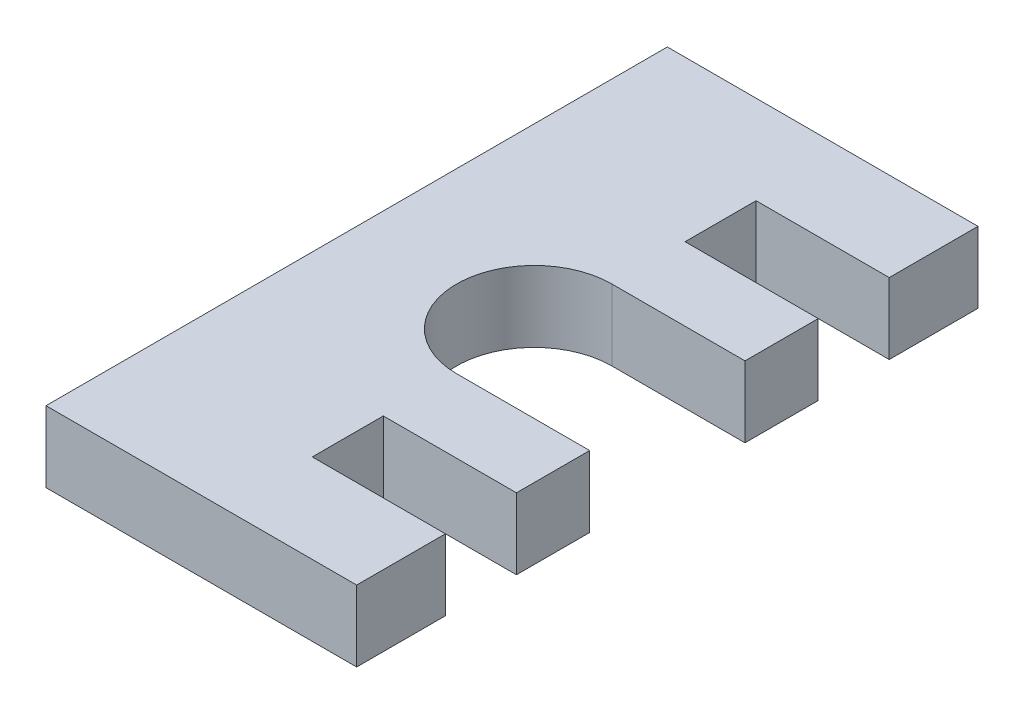
SolidWorks part; units mm, degrees
material "Pine"
ref_plane "Front Plane" through (0, 0, 0) normal (0, 0, 1) x (1, 0, 0)
ref_plane "Top Plane" through (0, 0, 0) normal (0, 1, 0) x (1, 0, 0)
ref_plane "Right Plane" through (0, 0, 0) normal (1, 0, 0) x (0, 0, -1)
sketch "Sketch1" plane through (0, 0, 0) normal (0, 1, 0) x (1, 0, 0)
  line L2 (22.225, 22.225) -> (22.225, 15.875)
  line L3 (22.225, 15.875) -> (12.7, 15.875)
  line L4 (12.7, 15.875) -> (12.7, 10.795)
  line L5 (12.7, 10.795) -> (22.225, 10.795)
  line L6 (22.225, 10.795) -> (22.225, 5.5562)
  line L7 (0, 0) -> (59.4192, 0) construction
  line L8 (22.225, -10.795) -> (22.225, -5.5562)
  line L9 (12.7, -10.795) -> (22.225, -10.795)
  line L10 (12.7, -15.875) -> (12.7, -10.795)
  line L11 (22.225, -15.875) -> (12.7, -15.875)
  line L12 (22.225, -22.225) -> (22.225, -15.875)
  line L15 (22.225, 5.5562) -> (12.7, 5.5563)
  line L16 (22.225, -5.5562) -> (12.7, -5.5562)
  line L21 (0, 0) -> (0, 22.225)
  line L22 (0, 22.225) -> (22.225, 22.225)
  line L23 (22.225, -22.225) -> (0, -22.225)
  line L24 (0, -22.225) -> (0, 0)
  arc A1 (12.7, 5.5563) -> (12.7, -5.5562) centre (12.7, 0) ccw
  dimension "D2" = 11.1125
  dimension "D1" = 5.08
  dimension "D3" = 6.35
  dimension "D5" = 31.75
extrude "Boss-Extrude1" add sketch "Sketch1" along normal blind 5.08
